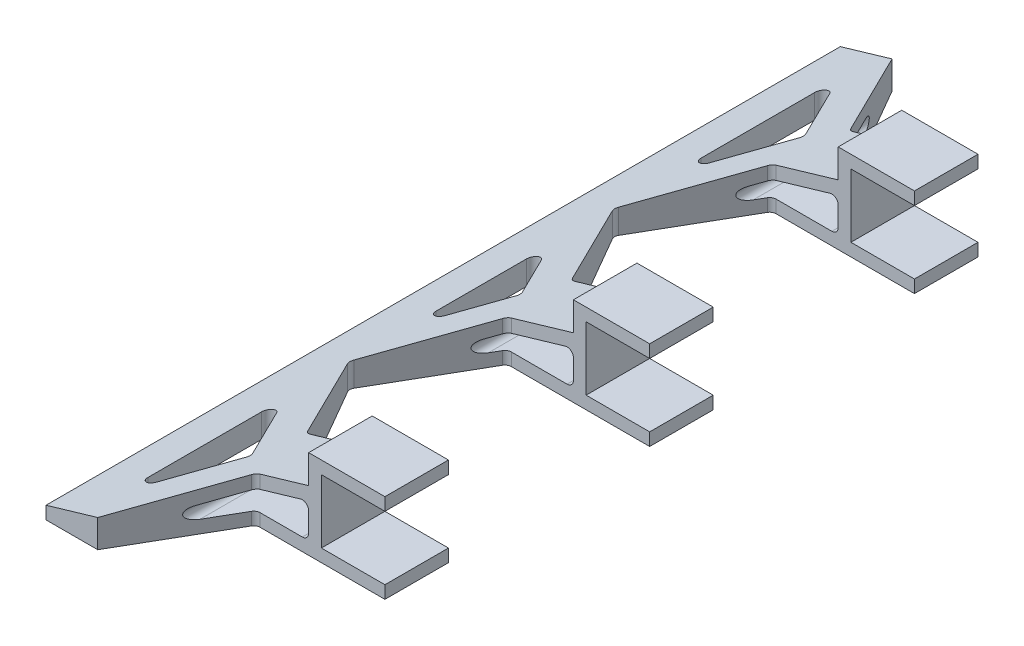
SolidWorks part; units mm, degrees
ref_plane "前视基准面" through (0, 0, 0) normal (0, 0, 1) x (1, 0, 0)
ref_plane "上视基准面" through (0, 0, 0) normal (0, 1, 0) x (1, 0, 0)
ref_plane "右视基准面" through (0, 0, 0) normal (1, 0, 0) x (0, 0, -1)
sketch "草图1" plane through (0, 0, 0) normal (1, 0, 0) x (0, 0, -1)
  line L1 (-40.6358, 16.9636) -> (209.3642, 16.9636)
  line L2 (-40.6358, 16.9636) -> (-40.6358, -11.0364)
  line L3 (-40.6358, -11.0364) -> (209.3642, -11.0364)
  line L4 (209.3642, 16.9636) -> (209.3642, -11.0364)
  line L5 (-40.6358, 12.9636) -> (209.3642, 12.9636)
  line L6 (-40.6358, 12.9636) -> (-40.6358, -7.0364)
  line L7 (-40.6358, -7.0364) -> (209.3642, -7.0364)
  line L8 (209.3642, 12.9636) -> (209.3642, -7.0364)
  dimension "D1" = 20
  dimension "D2" = 4
  dimension "D3" = 4
  dimension "D4" = 250
extrude "凸台-拉伸1" add sketch "草图1" along normal blind 20 contours L2 L5 L4 L1 | L7 L2 L3 L4
sketch "草图2" plane through (0, 0, 0) normal (-1, 0, 0) x (0, 0, 1)
  line L1 (-209.3642, 16.9636) -> (40.6358, 16.9636)
  line L2 (-209.3642, 16.9636) -> (-209.3642, -11.0364)
  line L3 (-209.3642, -11.0364) -> (40.6358, -11.0364)
  line L4 (40.6358, 16.9636) -> (40.6358, -11.0364)
extrude "凸台-拉伸2" add sketch "草图2" along normal blind 4
sketch "草图3" plane through (-4, 0, 0) normal (-1, 0, 0) x (0, 0, 1)
  line L0 (40.6358, -11.0364) -> (40.6358, 16.9636) construction
  line L1 (-209.3642, -11.0364) -> (40.6358, -11.0364)
  line L2 (-209.3642, -11.0364) -> (-209.3642, -7.0364)
  line L3 (-209.3642, -7.0364) -> (40.6358, -7.0364)
  line L4 (40.6358, -11.0364) -> (40.6358, -7.0364)
  dimension "D1" = 4
extrude "凸台-拉伸3" add sketch "草图3" along normal blind 51
sketch "草图5" plane through (0, 0, 40.6358) normal (0, 0, 1) x (1, 0, 0)
  line L0 (-4, -7.0364) -> (-55, -7.0364)
  line L1 (-55, -7.0364) -> (-4, 7.9636)
  line L2 (-4, -7.0364) -> (-4, 16.9636) construction
  line L3 (-4, 7.9636) -> (-4, -7.0364)
  dimension "D1" = 15
extrude "凸台-拉伸4" add sketch "草图5" against normal blind 250
ref_plane "基准面1" through (0, 0, -84.3642) normal (0, 0, -1) x (-1, 0, 0)
sketch "草图7" plane through (0, 16.9636, 0) normal (0, 1, 0) x (1, 0, 0)
  line L0 (-38.72, 209.3642) -> (-20.4373, 177.6975)
  line L1 (-4, 209.3642) -> (-55, 209.3642) construction
  line L2 (-20.4373, 177.6975) -> (20, 177.6975)
  line L3 (20, -40.6358) -> (20, 209.3642) construction
  line L4 (20, 177.6975) -> (20, 209.3642)
  line L5 (20, 209.3642) -> (-38.72, 209.3642)
  line L6 (20, 157.6975) -> (-24.7172, 157.6975)
  line L7 (-24.7172, 157.6975) -> (-43, 126.0308)
  line L8 (-43, 126.0308) -> (-24.7172, 94.3642)
  line L9 (-24.7172, 94.3642) -> (20, 94.3642)
  line L10 (20, 94.3642) -> (20, 157.6975)
  line L11 (-43, 196.7773) -> (-43, 146.0308)
  line L12 (-43, 146.0308) -> (-28.3508, 171.404)
  line L13 (-28.3508, 171.404) -> (-43, 196.7773)
  line L14 (-43, 106.0308) -> (-30.4907, 84.3642)
  line L15 (15.4, 84.3642) -> (-15.4, 84.3642) construction
  line L16 (-30.4907, 84.3642) -> (-43, 84.3642)
  line L17 (-43, 84.3642) -> (-43, 106.0308)
  line L18 (-55, -40.6358) -> (-55, 209.3642) construction
  point P21 (-35.6754, 184.0907)
  dimension "D1" = 10
  dimension "D2" = 10
  dimension "D3" = 10
  dimension "D4" = 60
  dimension "D5" = 120
  dimension "D6" = 30
  dimension "D7" = 120
  dimension "D8" = 12
  dimension "D9" = 12
  dimension "D10" = 20
  dimension "D11" = 10
  dimension "D12" = 31.6667
  dimension "D13" = 31.6667
extrude "切除-拉伸1" cut sketch "草图7" against normal blind 55
mirror "镜向1" about plane through (0, 0, -84.3642) normal (0, 0, -1) of "切除-拉伸1"
fillet "圆角1" radius 2 17 edges at (-43, -7.2717, -42.6975) (-43, -7.2717, -126.0308) (-20.4373, -3.9537, -177.6975) (-24.7172, -4.5831, -94.3642) (-24.7172, -4.5831, -157.6975) (-24.7172, -4.5831, -74.3642) (-20.4373, -3.9537, 8.9692) (-24.7172, -4.5831, -11.0308) (-43, -7.2717, 28.0489) (-43, -7.2717, -22.6975) (-28.3508, -5.1174, 2.6757) (-43, -7.2717, -62.6975) (-30.4907, -5.4321, -84.3642) (-43, -7.2717, -106.0308) (-43, -7.2717, -146.0308) (-43, -7.2717, -196.7773) (-28.3508, -5.1174, -171.404)
sketch "草图8" plane through (0, 0, -209.3642) normal (0, 0, -1) x (-1, 0, 0)
  line L0 (4, 1.1212) -> (4, -5.0364)
  line L1 (6, -7.0364) -> (26.9359, -7.0364)
  line L2 (27.5003, -3.1177) -> (6.5643, 3.0399)
  line L3 (19.2826, 3.4687) -> (4, 7.9636) construction
  line L4 (4, 7.9636) -> (4, 16.9636) construction
  line L5 (0, -7.0364) -> (-20, -7.0364) construction
  arc A0 (4, -5.0364) -> (6, -7.0364) centre (6, -5.0364) ccw
  arc A1 (26.9359, -7.0364) -> (27.5003, -3.1177) centre (26.9359, -5.0364) ccw
  arc A2 (4, 1.1212) -> (6.5643, 3.0399) centre (6, 1.1212) cw
  dimension "D2" = 2
  dimension "D1" = 4
extrude "切除-拉伸2" cut sketch "草图8" against normal blind 250
